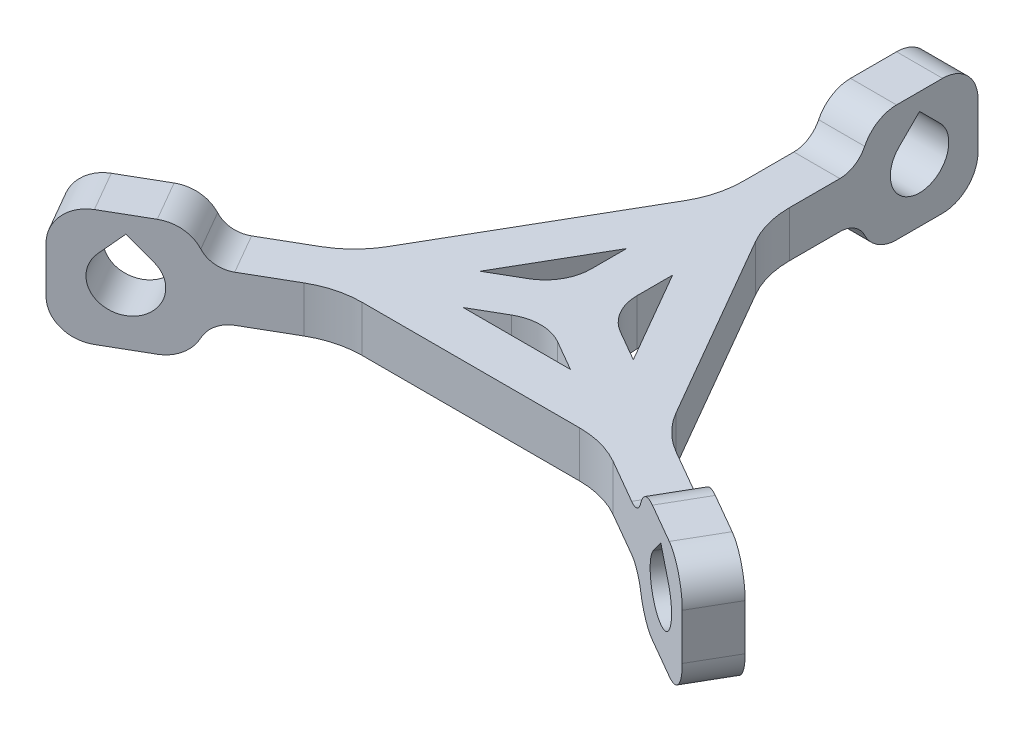
SolidWorks part; units mm, degrees
material "ABS"
ref_plane "Alzado" through (0, 0, 0) normal (0, 0, 1) x (1, 0, 0)
ref_plane "Planta" through (0, 0, 0) normal (0, 1, 0) x (1, 0, 0)
ref_plane "Vista lateral" through (0, 0, 0) normal (1, 0, 0) x (0, 0, -1)
sketch "Croquis1" plane through (0, 0, 0) normal (0, 1, 0) x (1, 0, 0)
  line L0 (0, 0) -> (0, 35) construction
  line L1 (0, 0) -> (-30.3109, -17.5) construction
  line L2 (0, 0) -> (30.3109, -17.5) construction
  line L3 (-2.5, 28.65) -> (2.5, 28.65)
  line L4 (2.5, 28.65) -> (2.5, 20.8494)
  line L5 (5, 0) -> (8.3253, -1.9199)
  line L6 (26.0616, -12.1599) -> (23.5616, -16.4901)
  line L7 (23.5616, -16.4901) -> (16.8061, -12.5897)
  line L8 (-2.5, -4.3301) -> (-5.8253, -6.25)
  line L9 (-23.5616, -16.4901) -> (-26.0616, -12.1599)
  line L10 (-26.0616, -12.1599) -> (-19.3061, -8.2596)
  line L11 (-2.5, 4.3301) -> (-2.5, 8.1699)
  line L12 (0, -2.8868) -> (0, 0) construction
  line L13 (0, 0) -> (-2.5, 1.4434) construction
  line L14 (0, 0) -> (2.5, 1.4434) construction
  line L15 (0, 17.5) -> (15.1554, -8.75) construction
  line L16 (0, 17.5) -> (-15.1554, -8.75) construction
  line L17 (-15.1554, -8.75) -> (15.1554, -8.75) construction
  line L18 (2.5, 8.1699) -> (8.3253, -1.9199)
  line L19 (3.8397, 15.8494) -> (15.6458, -4.5994)
  line L20 (-2.5, 8.1699) -> (-8.3253, -1.9199)
  line L21 (-3.8397, 15.8494) -> (-15.6458, -4.5994)
  line L22 (-5.8253, -6.25) -> (5.8253, -6.25)
  line L23 (-11.8061, -11.25) -> (11.8061, -11.25)
  line L24 (0, -6.25) -> (0, -11.25) construction
  line L25 (5.4127, 3.125) -> (9.7428, 5.625) construction
  line L26 (-5.4127, 3.125) -> (-9.7428, 5.625) construction
  line L27 (-2.5, 20.8494) -> (-2.5, 28.65)
  line L28 (2.5, 8.1699) -> (2.5, 4.3301)
  line L29 (19.3061, -8.2596) -> (26.0616, -12.1599)
  line L30 (5.8253, -6.25) -> (2.5, -4.3301)
  line L31 (-16.8061, -12.5897) -> (-23.5616, -16.4901)
  line L32 (-8.3253, -1.9199) -> (-5, 0)
  arc A0 (11.8061, -11.25) -> (16.8061, -12.5897) centre (11.8061, -21.25) cw
  arc A1 (15.6458, -4.5994) -> (19.3061, -8.2596) centre (24.3061, 0.4006) ccw
  arc A2 (-11.8061, -11.25) -> (-16.8061, -12.5897) centre (-11.8061, -21.25) ccw
  arc A3 (-15.6458, -4.5994) -> (-19.3061, -8.2596) centre (-24.3061, 0.4006) cw
  arc A4 (-3.8397, 15.8494) -> (-2.5, 20.8494) centre (-12.5, 20.8494) ccw
  arc A5 (3.8397, 15.8494) -> (2.5, 20.8494) centre (12.5, 20.8494) cw
  arc A6 (2.5, -4.3301) -> (-2.5, -4.3301) centre (0, -8.6603) ccw
  arc A7 (2.5, 4.3301) -> (5, 0) centre (7.5, 4.3301) ccw
  arc A8 (-5, 0) -> (-2.5, 4.3301) centre (-7.5, 4.3301) ccw
  point P8 (0, 28.65)
  point P12 (-24.8116, -14.325)
  point P18 (24.8116, -14.325)
  point P34 (0, -8.75)
  point P37 (7.5777, 4.375)
  point P38 (-7.5777, 4.375)
  point P46 (16.9856, -6.9199)
  point P49 (-14.4856, -11.25)
  point P54 (-2.5, 18.1699)
  dimension "D9" = 10
  dimension "D10" = 5
  dimension "D1" = 120
  dimension "D2" = 120
  dimension "D3" = 35
  dimension "D4" = 5
  dimension "D5" = 6.35
  dimension "D6" = 5
  dimension "D7" = 6.35
  dimension "D8" = 6.35
extrude "Saliente-Extruir1" add sketch "Croquis1" along normal mid plane 5
sketch "Croquis2" plane through (0, 0, 0) normal (0, 1, 0) x (1, 0, 0)
  line L1 (-2.5, 28.65) -> (2.5, 28.65)
  line L2 (-2.5, 28.65) -> (-2.5, 41.35)
  line L3 (-2.5, 41.35) -> (2.5, 41.35)
  line L4 (2.5, 28.65) -> (2.5, 41.35)
  dimension "D1" = 12.7
extrude "Saliente-Extruir2" add sketch "Croquis2" along normal mid plane 12.7
sketch "Croquis3" plane through (2.5, 0, 0) normal (1, 0, 0) x (0, 0, -1)
  line L1 (41.35, 6.35) -> (41.35, -6.35) construction
  line L2 (32.7549, 2.2451) -> (35, 4.4901)
  line L3 (35, 4.4901) -> (37.2451, 2.2451)
  arc A0 (32.7549, 2.2451) -> (37.2451, 2.2451) centre (35, 0) ccw
  dimension "D2" = 6.35
  dimension "D1" = 6.35
  dimension "D3" = 90
extrude "Cortar-Extruir1" cut sketch "Croquis3" against normal up to next
sketch "Croquis4" plane through (-2.5, 0, 0) normal (-1, 0, 0) x (0, 0, 1)
  line L0 (-41.35, 6.35) -> (-37.5, 6.35)
  line L1 (-41.35, 6.35) -> (-28.65, 6.35) construction
  line L3 (-41.35, 6.35) -> (-41.35, -6.35) construction
  line L4 (-41.35, 2.5) -> (-41.35, 6.35)
  line L6 (-32.5, 6.35) -> (-28.65, 6.35)
  line L7 (-28.65, 6.35) -> (-28.65, 2.5) construction
  line L8 (-28.65, 6.35) -> (-28.65, 2.5)
  line L10 (-41.35, -6.35) -> (-28.65, -6.35) construction
  line L12 (-41.35, -2.5) -> (-41.35, -6.35)
  line L13 (-41.35, -6.35) -> (-37.5, -6.35)
  line L14 (-28.65, -2.5) -> (-28.65, -6.35)
  line L15 (-28.65, -6.35) -> (-32.5, -6.35)
  arc A0 (-32.5, 6.35) -> (-28.65, 2.5) centre (-32.5, 2.5) cw
  arc A1 (-32.5, -6.35) -> (-28.65, -2.5) centre (-32.5, -2.5) ccw
  arc A2 (-37.5, 6.35) -> (-41.35, 2.5) centre (-37.5, 2.5) ccw
  arc A4 (-41.35, -2.5) -> (-37.5, -6.35) centre (-37.5, -2.5) ccw
extrude "Cortar-Extruir2" cut sketch "Croquis4" against normal up to next
pattern_circular "MatrizC7" count 3 every 120 about axis through (0, 0, 0) along (0, 1, 0) of "Saliente-Extruir2", "Cortar-Extruir1", "Cortar-Extruir2"
fillet "Redondeo3" radius 3 1 edges at (0, 2.5, -28.65)
fillet "Redondeo4" radius 3 1 edges at (-24.8116, 2.5, 14.325)
fillet "Redondeo5" radius 3 1 edges at (24.8116, 2.5, 14.325)
fillet "Redondeo6" radius 3 1 edges at (-24.8116, -2.5, 14.325)
fillet "Redondeo7" radius 3 1 edges at (0, -2.5, -28.65)
fillet "Redondeo8" radius 3 1 edges at (24.8116, -2.5, 14.325)
equation "\"D\"= 35"
equation "\"D3@Croquis1\"=\"D\""
equation "\"G\"=5"
equation "\"D4@Croquis1\"=\"G\""
equation "\"Da\"= 6.35"
equation "\"D5@Croquis1\"=\"Da\""
equation "\"D6@Croquis1\"=\"G\""
equation "\"D7@Croquis1\"=\"D5@Croquis1\""
equation "\"D8@Croquis1\"=\"D5@Croquis1\""
equation "\"D1@Saliente-Extruir1\"=\"G\""
equation "\"D1@Croquis2\"=\"Da\"*2"
equation "\"D1@Saliente-Extruir2\"=\"Da\"*2"
equation "\"D1@Croquis3\"=\"Da\""
equation "\"D2@Croquis3\"=\"Da\""
